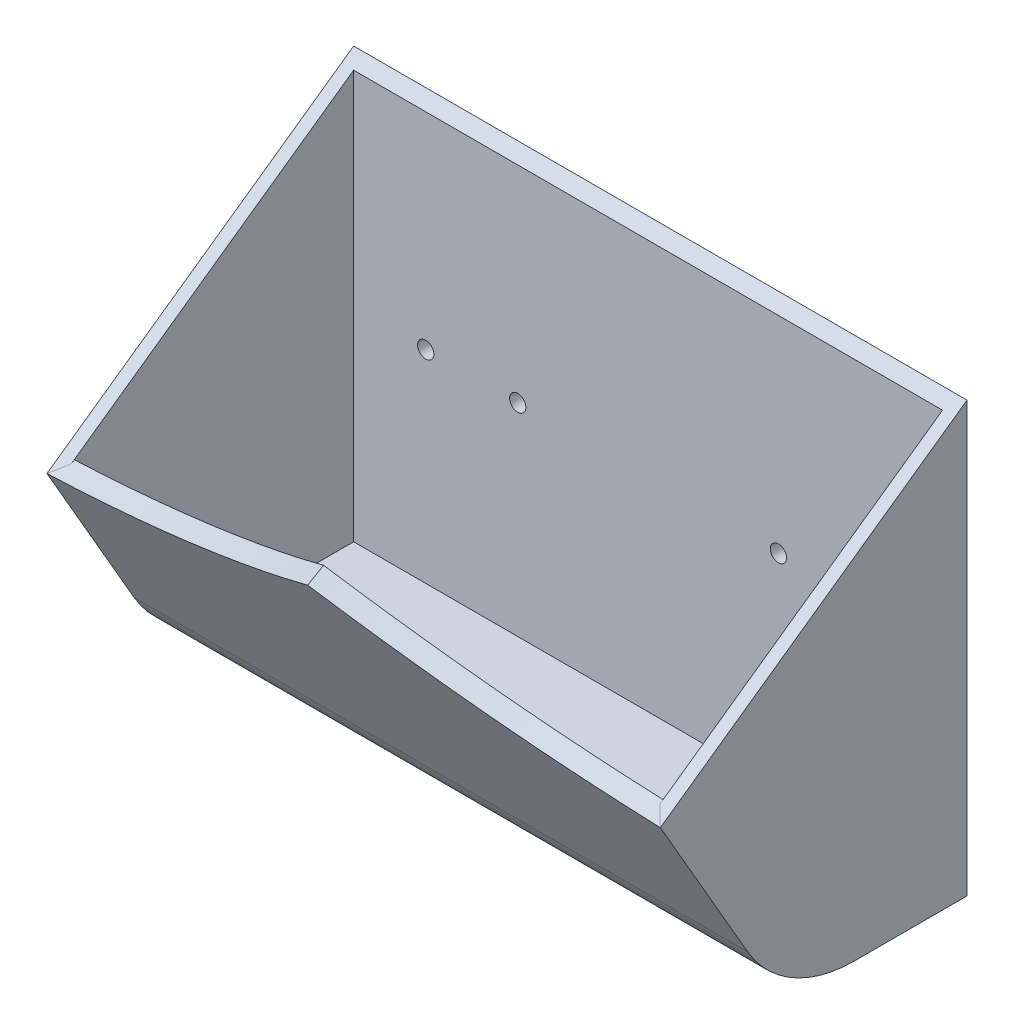
SolidWorks part; units mm, degrees
ref_plane "Front Plane" through (0, 0, 0) normal (0, 0, 1) x (1, 0, 0)
ref_plane "Top Plane" through (0, 0, 0) normal (0, 1, 0) x (1, 0, 0)
ref_plane "Right Plane" through (0, 0, 0) normal (1, 0, 0) x (0, 0, -1)
sketch "Sketch1" plane through (0, 0, 0) normal (0, 0, 1) x (1, 0, 0)
  line L1 (-76.2, 38.1) -> (76.2, 38.1)
  line L2 (-76.2, 38.1) -> (-76.2, -38.1)
  line L3 (-76.2, -38.1) -> (76.2, -38.1)
  line L4 (76.2, 38.1) -> (76.2, -38.1)
  line L5 (-76.2, 38.1) -> (76.2, -38.1) construction
  line L6 (-76.2, -38.1) -> (76.2, 38.1) construction
  point P0 (0, 0)
  dimension "D1" = 152.4
  dimension "D2" = 76.2
sketch "Sketch2" plane through (0, 0, 0) normal (1, 0, 0) x (0, 0, -1)
  line L0 (0, 50.8) -> (0, -38.1)
  line L1 (0, 38.1) -> (0, -38.1) construction
  line L2 (0, -38.1) -> (0, 38.1) construction
  line L3 (0, 38.1) -> (0, -38.1) construction
  line L4 (0, -38.1) -> (-38.1, -38.1)
  line L5 (-38.1, -38.1) -> (-63.5, 5.8941)
  line L6 (-63.5, 5.8941) -> (0, 50.8)
  dimension "D1" = 38.1
  dimension "D2" = 120
  dimension "D3" = 50.8
  dimension "D4" = 88.9
extrude "Boss-Extrude1" add sketch "Sketch2" along normal mid plane 127
fillet "Fillet1" radius 25.4 1 edges at (0, -38.1, 38.1)
sketch "Sketch3" plane through (0, -26.0228, 45.0728) normal (0, -0.5, 0.866) x (1, 0, 0)
  line L1 (63.5, 36.8544) -> (-63.5, 36.8544) construction
  line L3 (-63.5, 36.8544) -> (63.5, 36.8544)
  line L4 (0, 55.9044) -> (0, 0) construction
  arc A1 (0, 55.9044) -> (63.5, 36.8544) centre (81.9447, 213.6951) ccw
  arc A2 (-63.5, 36.8544) -> (0, 55.9044) centre (-81.9447, 213.6951) ccw
  dimension "D2" = 177.8
  dimension "D3" = 177.8
  dimension "D1" = 19.05
ref_plane "Plane1" through (0, -26.0228, 45.0728) normal (0, -0.5, 0.866) x (1, 0, 0)
shell "Shell1" thickness 2.54
extrude "Boss-Extrude4" add sketch "Sketch3" against normal blind 3.81
sketch "Sketch5" plane through (0, 0, 0) normal (0, 0, -1) x (-1, 0, 0)
  line L0 (0, 0) -> (-63.5, 0) construction
  line L1 (-63.5, -38.1) -> (-63.5, 50.8) construction
  line L2 (0, 0) -> (63.5, 0) construction
  line L3 (63.5, -38.1) -> (63.5, 50.8) construction
  line L4 (-63.5, 6.35) -> (63.5, 6.35) construction
  line L5 (-63.5, 50.8) -> (-63.5, -38.1) construction
  line L6 (-63.5, 50.8) -> (63.5, 50.8) construction
  line L7 (-63.5, -38.1) -> (63.5, -38.1) construction
  line L8 (55.88, 50.8) -> (55.88, -38.1) construction
  line L9 (-63.5, 15.875) -> (-63.5, -3.175)
  line L10 (-63.5, -3.175) -> (-38.1, -3.175)
  line L11 (-38.1, -3.175) -> (-38.1, 15.875)
  line L12 (-38.1, 15.875) -> (-63.5, 15.875)
  line L17 (0, 0) -> (0, 50.8)
  line L18 (0, 50.8) -> (0, -38.1)
  line L19 (-50.8, 15.875) -> (-50.8, -3.175) construction
  line L20 (38.1, -3.175) -> (38.1, 15.875)
  line L21 (63.5, -3.175) -> (38.1, -3.175)
  line L22 (63.5, 15.875) -> (63.5, -3.175)
  line L23 (38.1, 15.875) -> (63.5, 15.875)
  circle A0 centre (-55.88, 10.795) radius 2.54
  circle A1 centre (-44.45, 10.795) radius 2.54
  circle A2 centre (-44.45, 1.905) radius 2.54
  circle A3 centre (-55.88, 1.905) radius 2.54
  circle A4 centre (44.45, 1.905) radius 2.54
  circle A5 centre (55.88, 1.905) radius 2.54
  circle A6 centre (55.88, 10.795) radius 2.54
  circle A7 centre (44.45, 10.795) radius 2.54
  dimension "D9" = 5.08
  dimension "D10" = 5.08
  dimension "D13" = 5.08
  dimension "D14" = 5.08
  dimension "D1" = 6.35
  dimension "D2" = 0
  dimension "D3" = 7.62
  dimension "D4" = 19.05
  dimension "D5" = 25.4
  dimension "D6" = 9.525
  dimension "D11" = 6.35
  dimension "D12" = 6.35
  dimension "D15" = 5.08
  dimension "D16" = 5.08
  dimension "D17" = 5.08
  dimension "D18" = 5.08
  dimension "D19" = 7.62
  dimension "D20" = 7.62
sketch "Sketch6" plane through (0, 0, 0) normal (0, 0, -1) x (-1, 0, 0)
  line L0 (-63.5, 6.35) -> (63.5, 6.35) construction
  line L1 (-63.5, -38.1) -> (-63.5, 50.8) construction
  line L2 (63.5, -38.1) -> (63.5, 50.8) construction
  line L3 (-63.5, 10.3124) -> (63.5, 10.3124)
  line L4 (-63.5, 2.3876) -> (63.5, 2.3876)
  line L5 (-22.2123, 10.3124) -> (-22.2123, 2.3876)
  line L6 (22.2123, 10.3124) -> (22.2123, 2.3876)
  line L7 (-46.0375, 6.35) -> (-26.9875, 6.35)
  line L8 (26.9875, 6.35) -> (46.0375, 6.35)
  line L9 (-36.5125, 10.3124) -> (-36.5125, 2.3876) construction
  line L10 (36.5125, 10.3124) -> (36.5125, 2.3876) construction
  line L11 (0, 50.8) -> (0, -38.1) construction
  line L12 (-63.5, 50.8) -> (63.5, 50.8) construction
  line L13 (-63.5, -38.1) -> (63.5, -38.1) construction
  line L14 (-22.2123, 6.35) -> (0, 6.35)
  line L15 (0, 6.35) -> (22.2123, 6.35)
  circle A0 centre (-46.0375, 6.35) radius 1.6891
  circle A1 centre (-26.9875, 6.35) radius 1.6891
  circle A2 centre (26.9875, 6.35) radius 1.6891
  circle A3 centre (46.0375, 6.35) radius 1.6891
  point P36 (0, 0)
  dimension "D10" = 3.3782
  dimension "D11" = 3.3782
  dimension "D12" = 3.3782
  dimension "D13" = 3.3782
  dimension "D1" = 6.35
  dimension "D2" = 3.9624
  dimension "D3" = 3.9624
  dimension "D4" = 19.05
  dimension "D5" = 19.05
  dimension "D6" = 9.525
  dimension "D7" = 4.7752
  dimension "D8" = 4.7752
  dimension "D9" = 9.525
  dimension "D14" = 73.025
extrude "Cut-Extrude2" cut sketch "Sketch6" against normal up to next contours A0 | A1 | A2 | A3
